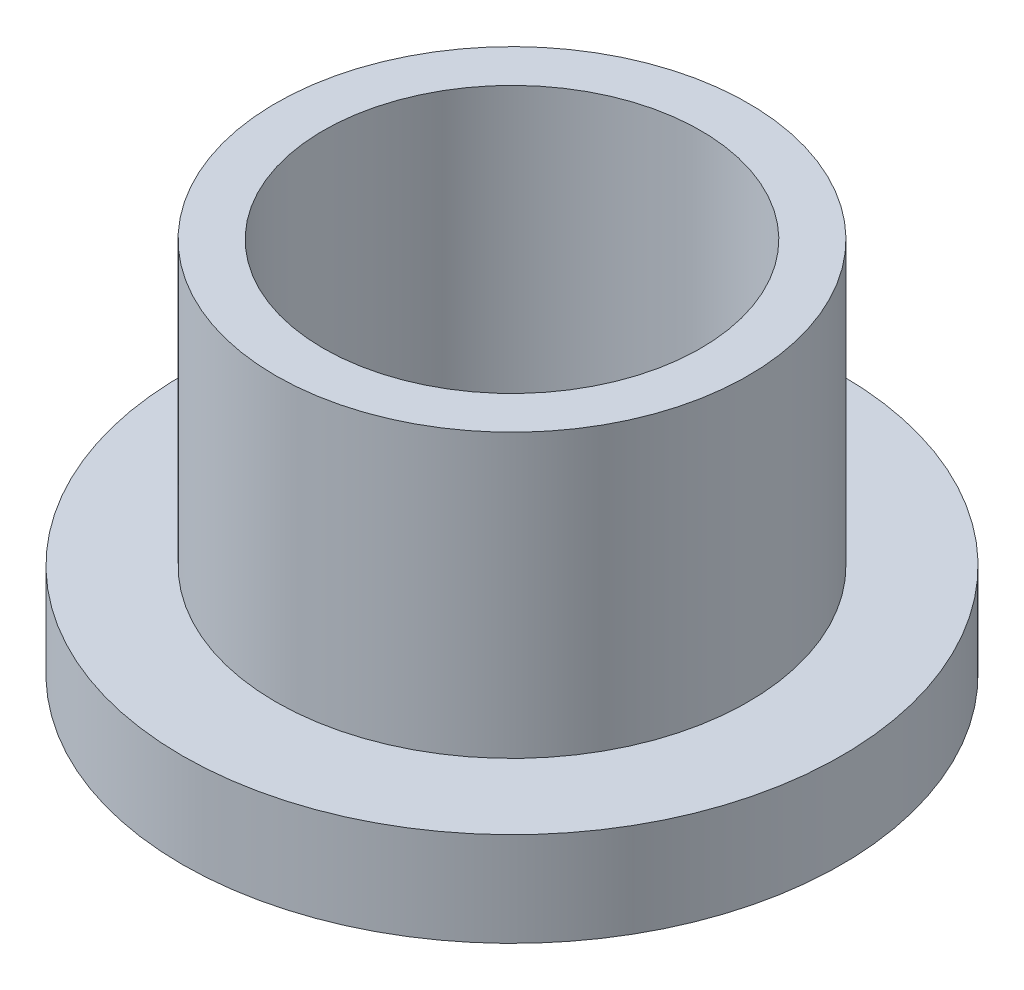
SolidWorks part; units mm, degrees
ref_plane "Front" through (0, 0, 0) normal (0, 0, 1) x (1, 0, 0)
ref_plane "Top" through (0, 0, 0) normal (0, 1, 0) x (1, 0, 0)
ref_plane "Right" through (0, 0, 0) normal (1, 0, 0) x (0, 0, -1)
sketch "Sketch1" plane through (0, 0, 0) normal (0, 1, 0) x (1, 0, 0)
  circle A0 centre (0, 0) radius 6.3627
  circle A1 centre (0, 0) radius 7.9629
  circle A2 centre (0, 0) radius 11.1125
  dimension "ID" = 12.7254
  dimension "OD" = 15.9258
  dimension "FlangeOD" = 22.225
sketch "Sketch2" plane through (0, 0, 0) normal (0, 1, 0) x (1, 0, 0)
  circle A0 centre (0, 0) radius 6.3627 construction
  circle A1 centre (0, 0) radius 7.9629 construction
  circle A2 centre (0, 0) radius 6.3627
  circle A3 centre (0, 0) radius 7.9629
extrude "Boss-Extrude1" add sketch "Sketch2" along normal blind 12.7
sketch "Sketch3" plane through (0, 0, 0) normal (0, 1, 0) x (1, 0, 0)
  circle A0 centre (0, 0) radius 11.1125 construction
  circle A1 centre (0, 0) radius 7.9629 construction
  circle A2 centre (0, 0) radius 11.1125
  circle A3 centre (0, 0) radius 7.9629
extrude "Boss-Extrude2" add sketch "Sketch3" along normal blind 3.175
